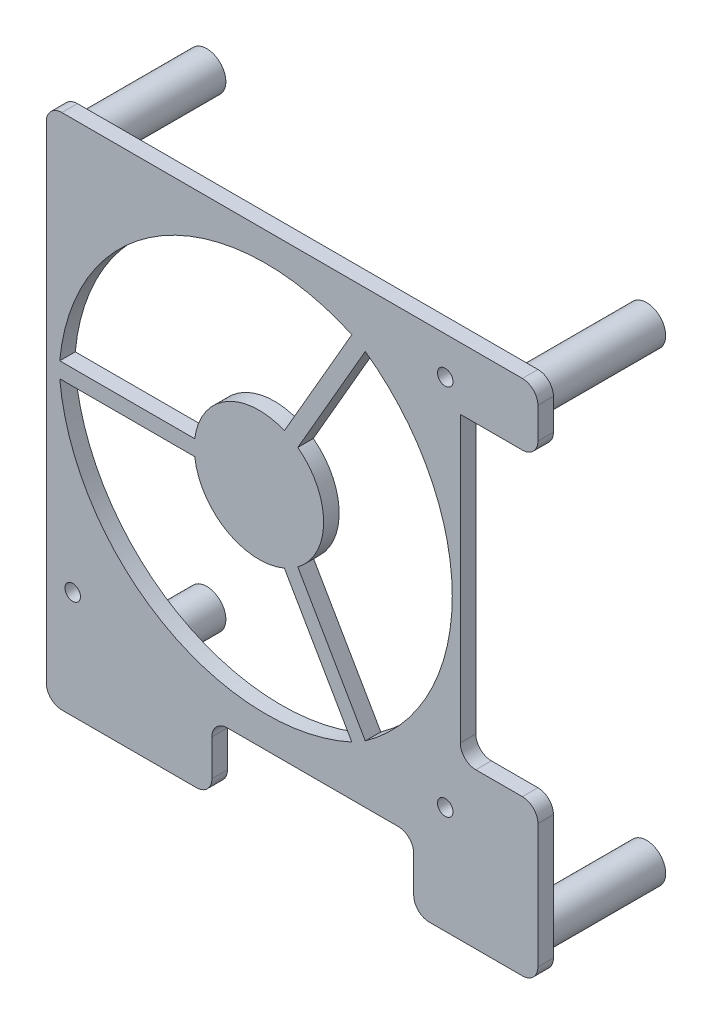
SolidWorks part; units mm, degrees
ref_plane "Alzado" through (0, 0, 0) normal (0, 0, 1) x (1, 0, 0)
ref_plane "Planta" through (0, 0, 0) normal (0, 1, 0) x (1, 0, 0)
ref_plane "Vista lateral" through (0, 0, 0) normal (1, 0, 0) x (0, 0, -1)
sketch "Croquis1" plane through (0, 0, 0) normal (0, 0, 1) x (1, 0, 0)
  line L0 (-194.105, 92.4709) -> (-194.105, 88.4709)
  line L1 (-191.105, 95.4709) -> (-102.105, 95.4709)
  line L2 (-99.105, 92.4709) -> (-99.105, 86.4709)
  line L3 (-140.5125, 52.2157) -> (-124.0125, 52.2157) construction
  line L4 (-102.105, -4.5291) -> (-120.105, -4.5291)
  line L5 (-194.105, 95.4709) -> (-99.105, -4.5291) construction
  line L6 (-194.105, -4.5291) -> (-99.105, 95.4709) construction
  line L7 (-194.105, 5.3828) -> (-194.105, 88.4709)
  line L8 (-153.0125, 52.2157) -> (-191.5125, 52.2157) construction
  line L9 (-181.9737, 53.7157) -> (-191.5125, 53.7157)
  line L10 (-139.831, 78.0468) -> (-137.2329, 76.5468) construction
  line L11 (-153.0125, 52.2157) -> (-133.7625, 85.5577) construction
  line L12 (-194.105, 5.3828) -> (-194.105, -1.5291)
  line L13 (-102.105, 83.4709) -> (-114.105, 83.4709)
  line L14 (-114.105, 60.4709) -> (-114.105, 83.4709)
  line L16 (-114.105, 60.4709) -> (-114.105, 28.4709)
  line L17 (-111.105, 25.4709) -> (-102.105, 25.4709)
  line L18 (-99.105, 22.4709) -> (-99.105, -1.5291)
  line L19 (-123.105, -1.5291) -> (-123.105, 5.4709)
  line L20 (-126.105, 8.4709) -> (-159.105, 8.4709)
  line L21 (-162.105, 5.4709) -> (-162.105, -1.5291)
  line L22 (-165.105, -4.5291) -> (-191.105, -4.5291)
  line L23 (-145.5086, 62.2128) -> (-137.2329, 76.5468)
  line L24 (-139.831, 78.0468) -> (-135.0616, 86.3077)
  line L25 (-137.2329, 76.5468) -> (-132.4635, 84.8077)
  line L26 (-145.5086, 42.2186) -> (-137.2329, 27.8846)
  line L27 (-183.0125, 82.2157) -> (-123.0125, 22.2157) construction
  line L28 (-183.0125, 22.2157) -> (-123.0125, 82.2157) construction
  line L29 (-132.2625, 52.2157) -> (-132.2625, 53.7157) construction
  line L30 (-137.2329, 27.8846) -> (-132.4635, 19.6237)
  line L31 (-132.2625, 52.2157) -> (-132.2625, 50.7157) construction
  line L32 (-165.4222, 53.7157) -> (-181.9737, 53.7157)
  line L33 (-148.1067, 40.7186) -> (-139.831, 26.3846)
  line L34 (-148.1067, 63.7128) -> (-139.831, 78.0468)
  line L35 (-139.831, 26.3846) -> (-135.0616, 18.1237)
  line L36 (-165.4222, 50.7157) -> (-181.9737, 50.7157)
  line L37 (-181.9737, 50.7157) -> (-191.5125, 50.7157)
  arc A0 (-194.105, 92.4709) -> (-191.105, 95.4709) centre (-191.105, 92.4709) cw
  arc A1 (-191.5125, 53.7157) -> (-135.0616, 86.3077) centre (-151.6942, 49.9322) cw
  arc A2 (-132.4635, 84.8077) -> (-132.4635, 19.6237) centre (-155.6492, 52.2157) cw
  arc A3 (-145.5086, 62.2128) -> (-145.5086, 42.2186) centre (-153.0125, 52.2157) cw
  arc A4 (-135.0616, 18.1237) -> (-191.5125, 50.7157) centre (-151.6942, 54.4991) cw
  arc A5 (-148.1067, 40.7186) -> (-165.4222, 50.7157) centre (-153.0125, 52.2157) cw
  arc A7 (-194.105, -1.5291) -> (-191.105, -4.5291) centre (-191.105, -1.5291) ccw
  arc A8 (-162.105, -1.5291) -> (-165.105, -4.5291) centre (-165.105, -1.5291) cw
  arc A9 (-159.105, 8.4709) -> (-162.105, 5.4709) centre (-159.105, 5.4709) ccw
  arc A10 (-123.105, 5.4709) -> (-126.105, 8.4709) centre (-126.105, 5.4709) ccw
  arc A11 (-120.105, -4.5291) -> (-123.105, -1.5291) centre (-120.105, -1.5291) cw
  arc A12 (-102.105, -4.5291) -> (-99.105, -1.5291) centre (-102.105, -1.5291) ccw
  arc A13 (-102.105, 25.4709) -> (-99.105, 22.4709) centre (-102.105, 22.4709) cw
  arc A14 (-114.105, 28.4709) -> (-111.105, 25.4709) centre (-111.105, 28.4709) ccw
  arc A18 (-99.105, 86.4709) -> (-102.105, 83.4709) centre (-102.105, 86.4709) cw
  arc A19 (-102.105, 95.4709) -> (-99.105, 92.4709) centre (-102.105, 92.4709) cw
  arc A22 (-165.4222, 53.7157) -> (-148.1067, 63.7128) centre (-153.0125, 52.2157) cw
  point P0 (-146.605, 45.4709)
  point P65 (-153.0125, 52.2157)
  point P86 (-153.0125, 52.2157)
  point P92 (-153.0125, 52.2157)
  dimension "D3" = 3
  dimension "D4" = 9.5388
  dimension "D5" = 9.5388
  dimension "D6" = 3
  dimension "D10" = 3
  dimension "D11" = 3
  dimension "D12" = 3
  dimension "D13" = 3
  dimension "D14" = 3
  dimension "D15" = 3
  dimension "D16" = 3
  dimension "D17" = 3
  dimension "D21" = 3
  dimension "D22" = 3
  dimension "D23" = 60
  dimension "D1" = 100
  dimension "D2" = 95
  dimension "D24" = 60
extrude "Saliente-Extruir1" add sketch "Croquis1" along normal blind 3
sketch "Croquis2" plane through (0, 0, 0) normal (0, 0, -1) x (-1, 0, 0)
  line L0 (194.105, 92.4709) -> (194.105, -1.5291) construction
  line L1 (102.105, 95.4709) -> (191.105, 95.4709) construction
  circle A0 centre (189.105, 90.4709) radius 3.7
  circle A1 centre (104.105, 90.4709) radius 3.7
  circle A2 centre (104.105, 0.4709) radius 3.7
  circle A3 centre (189.105, 0.4709) radius 3.7
  circle A4 centre (189.105, 90.4709) radius 1.5
  circle A5 centre (104.105, 90.4709) radius 1.5
  circle A6 centre (104.105, 0.4709) radius 1.5
  circle A7 centre (189.105, 0.4709) radius 1.5
  dimension "D1" = 5
  dimension "D5" = 2
  dimension "D2" = 5
  dimension "D3" = 2
  dimension "D4" = 2
  dimension "D6" = 2
extrude "Saliente-Extruir2" add sketch "Croquis2" along normal blind 23
sketch "Croquis3" plane through (0, 0, 3) normal (0, 0, 1) x (1, 0, 0)
  line L1 (-117.0125, 52.2157) -> (-117.0125, 88.2157) construction
  line L2 (-117.0125, 88.2157) -> (-189.0125, 88.2157) construction
  line L3 (-189.0125, 88.2157) -> (-189.0125, 16.2157) construction
  line L4 (-189.0125, 16.2157) -> (-117.0125, 16.2157) construction
  circle A0 centre (-117.0125, 16.2157) radius 1.5
  circle A1 centre (-189.0125, 16.2157) radius 1.5
  circle A3 centre (-117.0125, 88.2157) radius 1.5
  circle A4 centre (-189.0125, 88.2157) radius 1.5 [skipped]
  dimension "D1" = 2
  dimension "D2" = 2
extrude "Cortar-Extruir1" cut sketch "Croquis3" against normal up to vertex (3 mm away)
